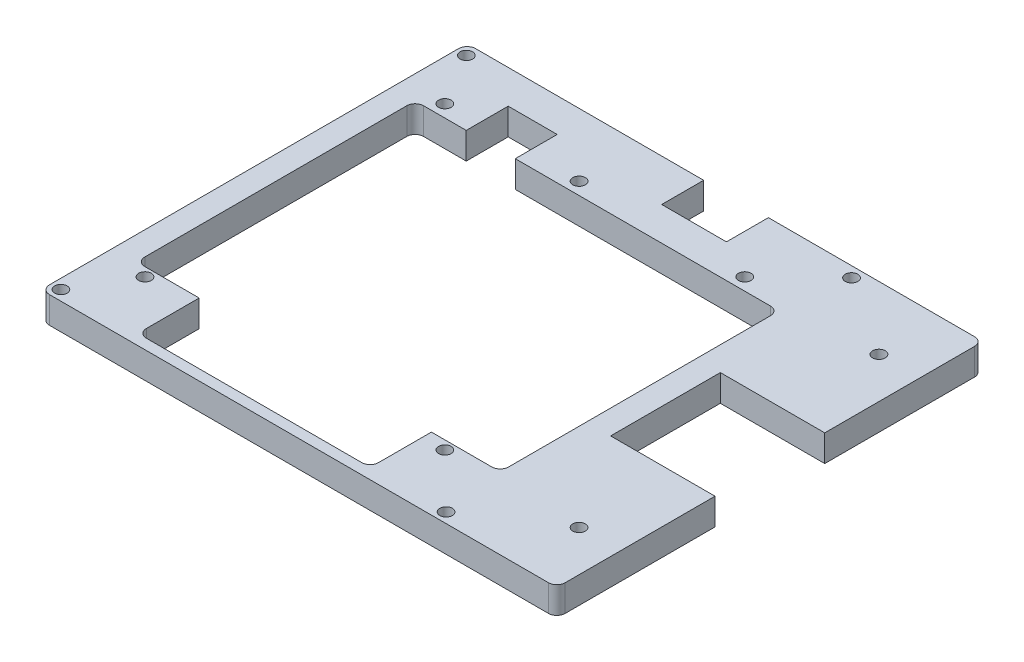
SolidWorks part; units mm, degrees
material "Acrylic (Medium-high impact)"
ref_plane "Front Plane" through (0, 0, 0) normal (0, 0, 1) x (1, 0, 0)
ref_plane "Top Plane" through (0, 0, 0) normal (0, 1, 0) x (1, 0, 0)
ref_plane "Right Plane" through (0, 0, 0) normal (1, 0, 0) x (0, 0, -1)
sketch "Sketch1" plane through (0, 0, 0) normal (0, 1, 0) x (1, 0, 0)
  line L0 (30.2159, 32.8) -> (-56.5147, 32.8)
  line L1 (30.2159, 32.8) -> (30.2159, -33.655)
  line L2 (30.2159, -33.655) -> (-56.5147, -33.655)
  line L3 (-60.1027, -50.8) -> (32.3533, -50.8)
  line L4 (34.3853, -48.768) -> (34.3853, 48.768)
  line L5 (32.3533, 50.8) -> (-60.1027, 50.8)
  line L6 (-62.1347, 48.768) -> (-62.1347, -48.768)
  line L7 (-56.5147, 32.8) -> (-56.5147, -33.655)
  line L8 (-41.5607, -33.655) -> (13.8113, -33.655)
  line L9 (-41.5607, -33.655) -> (-41.5607, -48.26)
  line L10 (-41.5607, -48.26) -> (13.8113, -48.26)
  line L11 (13.8113, -33.655) -> (13.8113, -48.26)
  line L12 (-44.3347, 32.8) -> (-32.6472, 32.8)
  line L13 (-44.3347, 32.8) -> (-44.3347, 42.8)
  line L14 (-44.3347, 42.8) -> (-32.6472, 42.8)
  line L15 (-32.6472, 32.8) -> (-32.6472, 42.8)
  line L16 (-5.7267, 50.8) -> (9.7073, 50.8)
  line L17 (-5.7267, 50.8) -> (-5.7267, 40.8)
  line L18 (-5.7267, 40.8) -> (9.7073, 40.8)
  line L19 (9.7073, 50.8) -> (9.7073, 40.8)
  line L20 (60.8652, 44) -> (-62.1348, 44)
  line L21 (60.8652, 44) -> (60.8653, -44)
  line L22 (60.8653, -44) -> (-62.1347, -44)
  line L23 (-62.1348, 44) -> (-62.1347, -44)
  line L24 (60.8652, 44) -> (-62.1347, -44) construction
  line L25 (60.8653, -44) -> (-62.1348, 44) construction
  line L26 (62.1348, -13.081) -> (35.9727, -13.081)
  line L27 (62.1348, -13.081) -> (62.1348, 13.081)
  line L28 (62.1348, 13.081) -> (35.9727, 13.081)
  line L29 (35.9727, -13.081) -> (35.9727, 13.081)
  line L30 (62.1348, -13.081) -> (35.9727, 13.081) construction
  line L31 (62.1348, 13.081) -> (35.9727, -13.081) construction
  line L32 (34.3853, -48.768) -> (34.3853, 48.768)
  line L33 (34.3853, -48.768) -> (34.3853, 48.768)
  line L34 (-60.1027, -50.8) -> (60.8653, -50.8)
  line L35 (60.8653, -50.8) -> (60.8652, 50.8)
  line L36 (60.8652, 50.8) -> (32.3533, 50.8)
  circle A0 centre (-52.3847, 35.75) radius 1.5
  circle A1 centre (-20.3847, 35.75) radius 1.5
  circle A2 centre (19.1153, 35.75) radius 1.5
  circle A3 centre (51.1153, 35.75) radius 1.5
  arc A4 (-62.1347, -48.768) -> (-60.1027, -50.8) centre (-60.1027, -48.768) ccw
  arc A5 (32.3533, -50.8) -> (34.3853, -48.768) centre (32.3533, -48.768) ccw
  arc A6 (34.3853, 48.768) -> (32.3533, 50.8) centre (32.3533, 48.768) ccw
  arc A7 (-60.1027, 50.8) -> (-62.1347, 48.768) centre (-60.1027, 48.768) ccw
  circle A8 centre (51.1153, -35.75) radius 1.5
  circle A9 centre (19.1153, -35.75) radius 1.5
  circle A10 centre (-20.3847, -35.75) radius 1.5
  circle A11 centre (-52.3847, -35.75) radius 1.5
  point P28 (-0.6348, 0)
  point P34 (49.0538, 0)
  dimension "D13" = 3
  dimension "D1" = 96.52
  dimension "D2" = 101.6
  dimension "D3" = 10
  dimension "D4" = 10
  dimension "D5" = 8
  dimension "D6" = 88
  dimension "D7" = 123
  dimension "D8" = 26.162
  dimension "D9" = 26.162
  dimension "D10" = 1.5875
  dimension "D11" = 8.25
  dimension "D12" = 9.75
extrude "Boss-Extrude1" add sketch "Sketch1" along normal blind 6.35 contours L22 L4 L20 L19 L18 L17 L6 L9 L2 L7 L0 L13 L14 L15 L1 L11 A9 A2 A1 A0 A11 | L3 A5 L4 L22 L11 L10 L9 L6 A4 | L5 A7 L6 L20 L17 | L4 A6 L5 L19 L20 | A6 L4 L20 L35 L36 | L26 L29 L28 L21 L20 L4 L22 A3 A8 | A5 L34 L35 L22 L4
fillet "Fillet1" radius 2 8 edges at (60.8652, 3.175, -50.8) (60.8653, 3.175, 50.8) (30.2159, 3.175, 33.655) (13.8113, 3.175, 48.26) (-41.5607, 3.175, 48.26) (-56.5147, 3.175, 33.655) (30.2159, 3.175, -32.8) (-56.5147, 3.175, -32.8)
sketch "Sketch2" plane through (0, 6.35, 0) normal (0, 1, 0) x (1, 0, 0)
  line L0 (-60.1027, -50.8) -> (58.8653, -50.8) construction
  line L1 (-62.1347, 48.768) -> (-62.1347, -48.768) construction
  line L3 (-59.7971, -48.3934) -> (32.0476, -48.3934) construction
  line L4 (-59.7971, -48.3934) -> (-59.7971, 48.2853) construction
  line L5 (-59.7971, 48.2853) -> (32.0476, 48.2853) construction
  line L6 (32.0476, -48.3934) -> (32.0476, 48.2853) construction
  circle A0 centre (-59.7971, -48.3934) radius 1.5
  circle A1 centre (32.0476, -48.3934) radius 1.5
  circle A2 centre (32.0476, 48.2853) radius 1.5
  circle A3 centre (-59.7971, 48.2853) radius 1.5
  dimension "D3" = 3
  dimension "D1" = 2.4066
  dimension "D2" = 2.3376
  dimension "D4" = 96.6787
  dimension "D5" = 91.8447
extrude "Cut-Extrude1" cut sketch "Sketch2" against normal through all contours L4 L3 L6 L5
